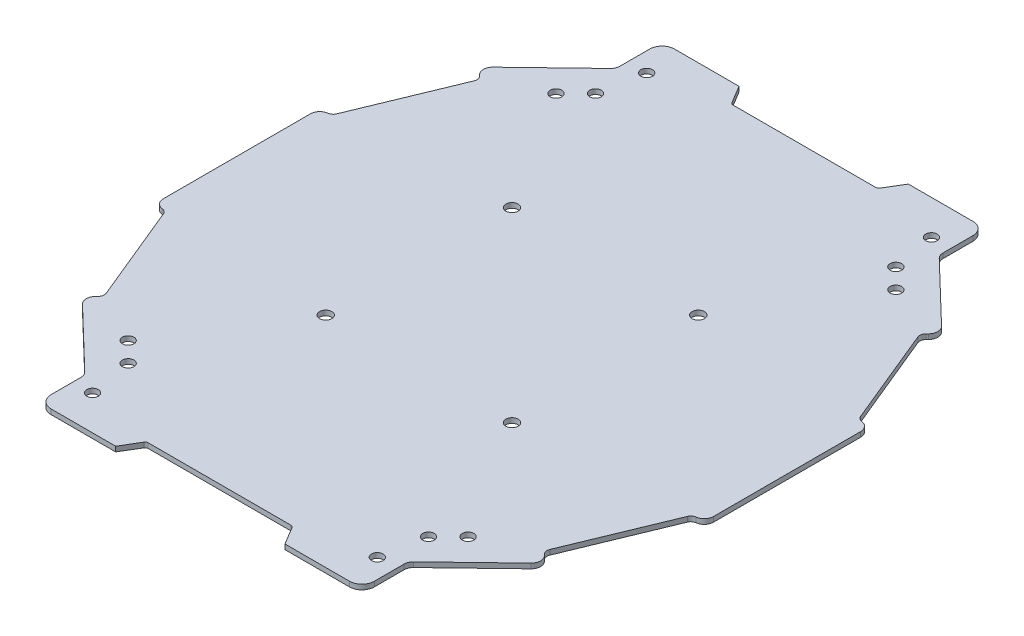
SolidWorks part; units mm, degrees
ref_plane "Front Plane" through (0, 0, 0) normal (0, 0, 1) x (1, 0, 0)
ref_plane "Top Plane" through (0, 0, 0) normal (0, 1, 0) x (1, 0, 0)
ref_plane "Right Plane" through (0, 0, 0) normal (1, 0, 0) x (0, 0, -1)
ref_plane "Plane1"
sketch "Sketch1" plane through (0, 0, 0) normal (0, 1, 0) x (-1, 0, 0)
  line L0 (74.0875, 321.0883) -> (70.3692, 327.2855)
  line L1 (70.3692, 327.2855) -> (45.5805, 327.2855)
  line L2 (45.5805, 327.2855) -> (45.5805, 312.4122)
  line L3 (45.5805, 312.4122) -> (23.246, 290.9343)
  line L4 (23.246, 290.9343) -> (26.6825, 287.3608)
  line L5 (26.6825, 287.3608) -> (12.7354, 253.539)
  line L6 (12.7354, 253.539) -> (9.0171, 253.539)
  line L7 (9.0171, 253.539) -> (9.0171, 226.8911)
  line L8 (9.0171, 226.8911) -> (9.0171, 200.2432)
  line L9 (9.0171, 200.2432) -> (12.7354, 200.2432)
  line L10 (12.7354, 200.2432) -> (26.6825, 166.4214)
  line L11 (26.6825, 166.4214) -> (23.246, 162.8479)
  line L12 (23.246, 162.8479) -> (45.5805, 141.37)
  line L13 (45.5805, 141.37) -> (45.5805, 126.4967)
  line L14 (45.5805, 126.4967) -> (70.3692, 126.4967)
  line L15 (70.3692, 126.4967) -> (74.0875, 132.6939)
  line L16 (74.0875, 132.6939) -> (97.6368, 132.6939)
  line L17 (97.6368, 132.6939) -> (121.1861, 132.6939)
  line L18 (121.1861, 132.6939) -> (124.9044, 126.4967)
  line L19 (124.9044, 126.4967) -> (149.6932, 126.4967)
  line L20 (149.6932, 126.4967) -> (149.6932, 141.37)
  line L21 (149.6932, 141.37) -> (172.0276, 162.8479)
  line L22 (172.0276, 162.8479) -> (168.5911, 166.4214)
  line L23 (168.5911, 166.4214) -> (182.5382, 200.2432)
  line L24 (182.5382, 200.2432) -> (186.2565, 200.2432)
  line L25 (186.2565, 200.2432) -> (186.2565, 226.8911)
  line L26 (186.2565, 226.8911) -> (186.2565, 253.539)
  line L27 (186.2565, 253.539) -> (182.5382, 253.539)
  line L28 (182.5382, 253.539) -> (168.5911, 287.3608)
  line L29 (168.5911, 287.3608) -> (172.0276, 290.9343)
  line L30 (172.0276, 290.9343) -> (149.6932, 312.4122)
  line L31 (149.6932, 312.4122) -> (149.6932, 327.2855)
  line L32 (149.6932, 327.2855) -> (124.9044, 327.2855)
  line L33 (124.9044, 327.2855) -> (121.1861, 321.0883)
  line L34 (121.1861, 321.0883) -> (97.6368, 321.0883)
  line L35 (97.6368, 321.0883) -> (74.0875, 321.0883)
  line L36 (97.6368, 132.6939) -> (97.6368, 321.0883) construction
  line L37 (9.0171, 226.8911) -> (186.2565, 226.8911) construction
  line L38 (67.6368, 256.8911) -> (127.6368, 196.8911) construction
  line L39 (127.6368, 256.8911) -> (67.6368, 196.8911) construction
  line L40 (42.8881, 295.782) -> (49.2662, 302.1601) construction
  line L41 (146.0075, 302.1601) -> (152.3856, 295.782) construction
  line L42 (49.2662, 151.6221) -> (42.8881, 158.0002) construction
  line L43 (146.0075, 151.6221) -> (152.3856, 158.0002) construction
  line L126 (176.3908, 226.8911) -> (176.3908, 225.1916)
  circle A1 centre (49.2662, 151.6221) radius 1.8592
  circle A22 centre (51.7777, 316.1305) radius 1.8592
  circle A23 centre (49.2662, 302.1601) radius 1.8592
  circle A27 centre (143.496, 137.6517) radius 1.8592
  circle A28 centre (146.0075, 151.6221) radius 1.8592
  circle A30 centre (143.496, 316.1305) radius 1.8592
  circle A54 centre (146.0075, 302.1601) radius 1.8592
  circle A77 centre (51.7777, 137.6517) radius 1.8592
  circle A78 centre (67.6368, 196.8911) radius 1.9831
  circle A79 centre (67.6368, 256.8911) radius 1.9831
  circle A82 centre (42.8881, 158.0002) radius 1.8592
  circle A86 centre (152.3856, 295.782) radius 1.8592
  circle A87 centre (42.8881, 295.782) radius 1.8592
  circle A90 centre (127.6368, 256.8911) radius 1.9831
  circle A91 centre (152.3856, 158.0002) radius 1.8592
  circle A96 centre (127.6368, 196.8911) radius 1.9831
  dimension "D1" = 30
  dimension "D28" = 6.1972
  dimension "D2" = 30
  dimension "D3" = 30
  dimension "D4" = 30
  dimension "D7" = 30
  dimension "D8" = 30
  dimension "D9" = 30
  dimension "D10" = 30
  dimension "D16" = 9.02
  dimension "D17" = 9.02
  dimension "D18" = 9.02
  dimension "D19" = 9.02
  dimension "D20" = 10
  dimension "D21" = 10
  dimension "D22" = 10
  dimension "D23" = 10
  dimension "D24" = 45
  dimension "D25" = 45
  dimension "D26" = 45
  dimension "D27" = 45
extrude "Extrusion1" add sketch "Sketch1" along normal blind 1.6
fillet "Fillet1" radius 1 4 edges at (-121.1861, 0.8, 132.6939) (-74.0875, 0.8, 132.6939) (-74.0875, 0.8, 321.0883) (-121.1861, 0.8, 321.0883)
fillet "Fillet2" radius 4 4 edges at (-149.6932, 0.8, 126.4967) (-45.5805, 0.8, 126.4967) (-149.6932, 0.8, 327.2855) (-45.5805, 0.8, 327.2855)
fillet "Fillet3" radius 3 4 edges at (-149.6932, 0.8, 141.37) (-45.5805, 0.8, 141.37) (-45.5805, 0.8, 312.4122) (-149.6932, 0.8, 312.4122)
fillet "Fillet4" radius 3 1 edges at (-172.0276, 0.8, 290.9343)
fillet "Fillet5" radius 2 1 edges at (-168.5911, 0.8, 287.3608)
fillet "Fillet6" radius 2 1 edges at (-26.6825, 0.8, 287.3608)
fillet "Fillet7" radius 3 1 edges at (-23.246, 0.8, 290.9343)
fillet "Fillet8" radius 3 2 edges at (-172.0276, 0.8, 162.8479) (-23.246, 0.8, 162.8479)
fillet "Fillet9" radius 2 2 edges at (-26.6825, 0.8, 166.4214) (-168.5911, 0.8, 166.4214)
fillet "Fillet10" radius 2 4 edges at (-12.7354, 0.8, 200.2432) (-12.7354, 0.8, 253.539) (-182.5382, 0.8, 253.539) (-182.5382, 0.8, 200.2432)
fillet "Fillet11" radius 3 4 edges at (-186.2565, 0.8, 200.2432) (-186.2565, 0.8, 253.539) (-9.0171, 0.8, 253.539) (-9.0171, 0.8, 200.2432)
